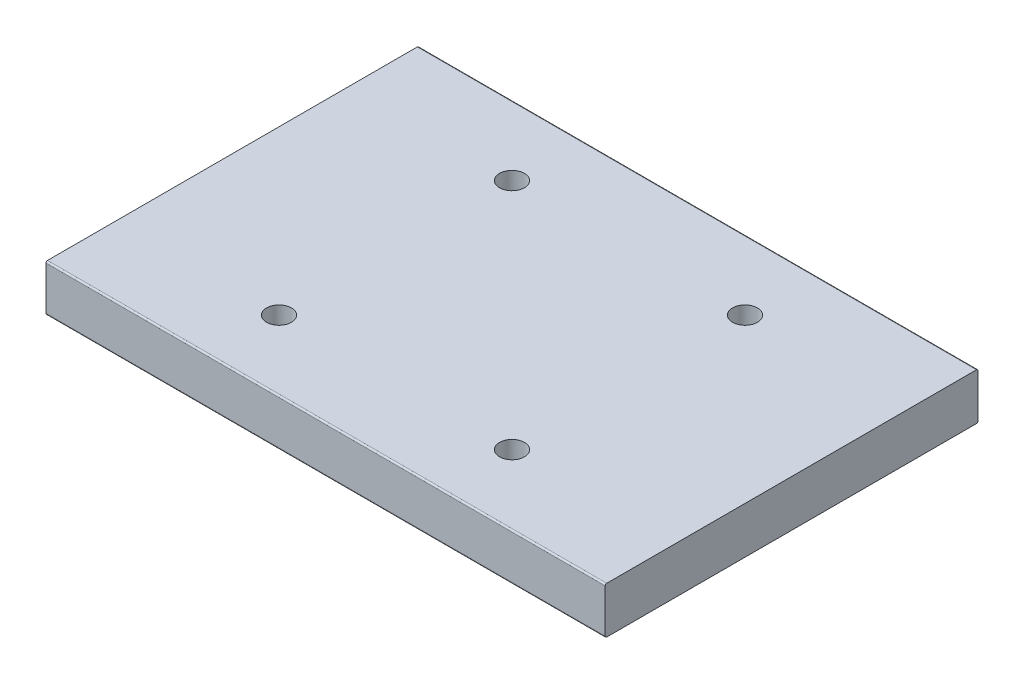
SolidWorks part; units mm, degrees
ref_plane "Front Plane" through (0, 0, 0) normal (0, 0, 1) x (1, 0, 0)
ref_plane "Top Plane" through (0, 0, 0) normal (0, 1, 0) x (1, 0, 0)
ref_plane "Right Plane" through (0, 0, 0) normal (1, 0, 0) x (0, 0, -1)
sketch "Sketch1" plane through (0, 0, 0) normal (0, 1, 0) x (1, 0, 0)
  line L1 (-76.2, -50.8) -> (76.2, -50.8) construction
  line L2 (-76.2, -50.8) -> (-76.2, 50.8) construction
  line L3 (-76.2, 50.8) -> (76.2, 50.8) construction
  line L4 (76.2, -50.8) -> (76.2, 50.8) construction
  line L5 (-76.2, -50.8) -> (76.2, 50.8) construction
  line L6 (-76.2, 50.8) -> (76.2, -50.8) construction
  point P0 (0, 0)
  dimension "Length" = 152.4
  dimension "Width" = 101.6
sketch "Sketch2" plane through (0, 0, 0) normal (1, 0, 0) x (0, 0, -1)
  line L0 (50.8, 6.35) -> (50.8, -6.35) construction
  dimension "Thickness" = 12.7
sketch "Sketch3" plane through (0, 0, 0) normal (0, 1, 0) x (1, 0, 0)
  line L1 (-76.2, 50.8) -> (76.2, 50.8)
  line L2 (-76.2, 50.8) -> (-76.2, -50.8)
  line L3 (-76.2, -50.8) -> (76.2, -50.8)
  line L4 (76.2, 50.8) -> (76.2, -50.8)
extrude "Boss-Extrude1" add sketch "Sketch3" along normal up to vertex (6.35 mm away) and the other way up to vertex (6.35 mm away) up to point (0, 6.35, -50.8) other way up to point (0, -6.35, -50.8)
fillet "Fillet1" radius 0.4191 4 edges at (0, -6.35, -50.8) (0, 6.35, -50.8) (0, -6.35, 50.8) (0, 6.35, 50.8)
sketch "Sketch5" plane through (0, 6.35, 0) normal (0, 1, 0) x (1, 0, 0)
  circle A0 centre (31.75, 31.75) radius 3.4036
  circle A1 centre (31.75, -31.75) radius 3.4036
  circle A2 centre (-31.75, -31.75) radius 3.4036
  circle A3 centre (-31.75, 31.75) radius 3.4036
  point P2 (0, 0)
  point P13 (0, 0)
  dimension "D1" = 6.8072
  dimension "D2" = 31.75
  dimension "D3" = 31.75
  dimension "D4" = 4
extrude "Cut-Extrude2" cut sketch "Sketch5" against normal through all
equation "\"D1@Fillet1\"=\"Thickness@Sketch2\"*.033"
